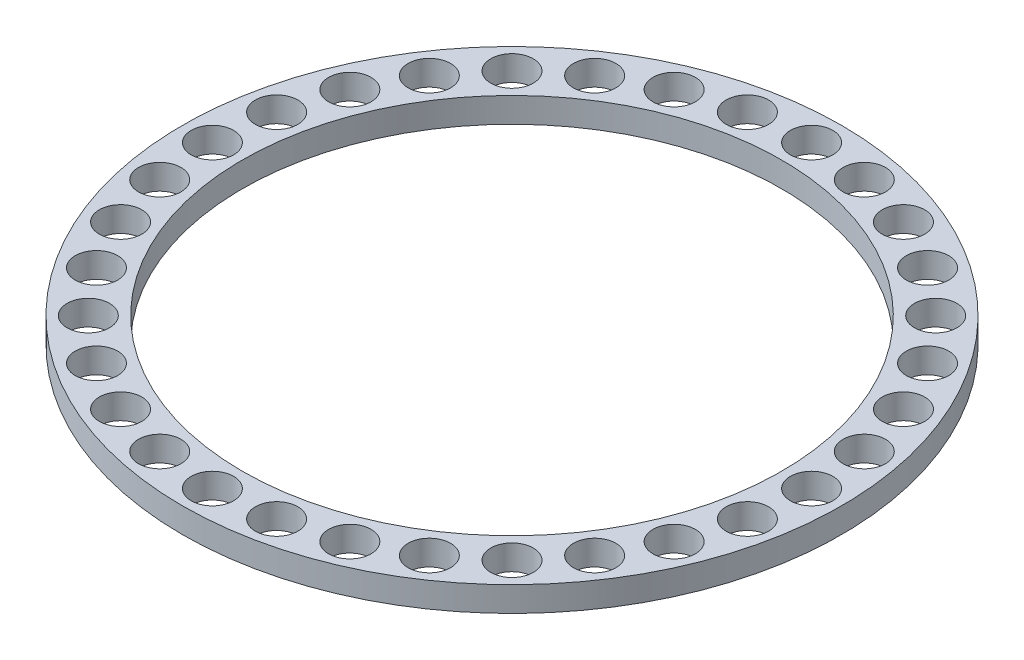
SolidWorks part; units mm, degrees
material "ABS"
ref_plane "Front Plane" through (0, 0, 0) normal (0, 0, 1) x (1, 0, 0)
ref_plane "Top Plane" through (0, 0, 0) normal (0, 1, 0) x (1, 0, 0)
ref_plane "Right Plane" through (0, 0, 0) normal (1, 0, 0) x (0, 0, -1)
sketch "Sketch1" plane through (0, 0, 0) normal (0, 1, 0) x (1, 0, 0)
  circle A0 centre (0, 0) radius 66
  circle A1 centre (0, 0) radius 54
  circle A2 centre (0, 0) radius 60 construction
  circle A3 centre (0, 60) radius 4.25
  circle A4 centre (11.7054, 58.8471) radius 4.25
  circle A5 centre (22.961, 55.4328) radius 4.25
  circle A6 centre (33.3342, 49.8882) radius 4.25
  circle A7 centre (42.4264, 42.4264) radius 4.25
  circle A8 centre (49.8882, 33.3342) radius 4.25
  circle A9 centre (55.4328, 22.961) radius 4.25
  circle A10 centre (58.8471, 11.7054) radius 4.25
  circle A11 centre (60, 0) radius 4.25
  circle A12 centre (58.8471, -11.7054) radius 4.25
  circle A13 centre (55.4328, -22.961) radius 4.25
  circle A14 centre (49.8882, -33.3342) radius 4.25
  circle A15 centre (42.4264, -42.4264) radius 4.25
  circle A16 centre (33.3342, -49.8882) radius 4.25
  circle A17 centre (22.961, -55.4328) radius 4.25
  circle A18 centre (11.7054, -58.8471) radius 4.25
  circle A19 centre (0, -60) radius 4.25
  circle A20 centre (-11.7054, -58.8471) radius 4.25
  circle A21 centre (-22.961, -55.4328) radius 4.25
  circle A22 centre (-33.3342, -49.8882) radius 4.25
  circle A23 centre (-42.4264, -42.4264) radius 4.25
  circle A24 centre (-49.8882, -33.3342) radius 4.25
  circle A25 centre (-55.4328, -22.961) radius 4.25
  circle A26 centre (-58.8471, -11.7054) radius 4.25
  circle A27 centre (-60, 0) radius 4.25
  circle A28 centre (-58.8471, 11.7054) radius 4.25
  circle A29 centre (-55.4328, 22.961) radius 4.25
  circle A30 centre (-49.8882, 33.3342) radius 4.25
  circle A31 centre (-42.4264, 42.4264) radius 4.25
  circle A32 centre (-33.3342, 49.8882) radius 4.25
  circle A33 centre (-22.961, 55.4328) radius 4.25
  circle A34 centre (-11.7054, 58.8471) radius 4.25
  point P72 (0, 0)
  dimension "D1" = 120
  dimension "D2" = 6
  dimension "D3" = 6
  dimension "D4" = 8.5
  dimension "D5" = 32
extrude "Boss-Extrude1" add sketch "Sketch1" along normal blind 5
